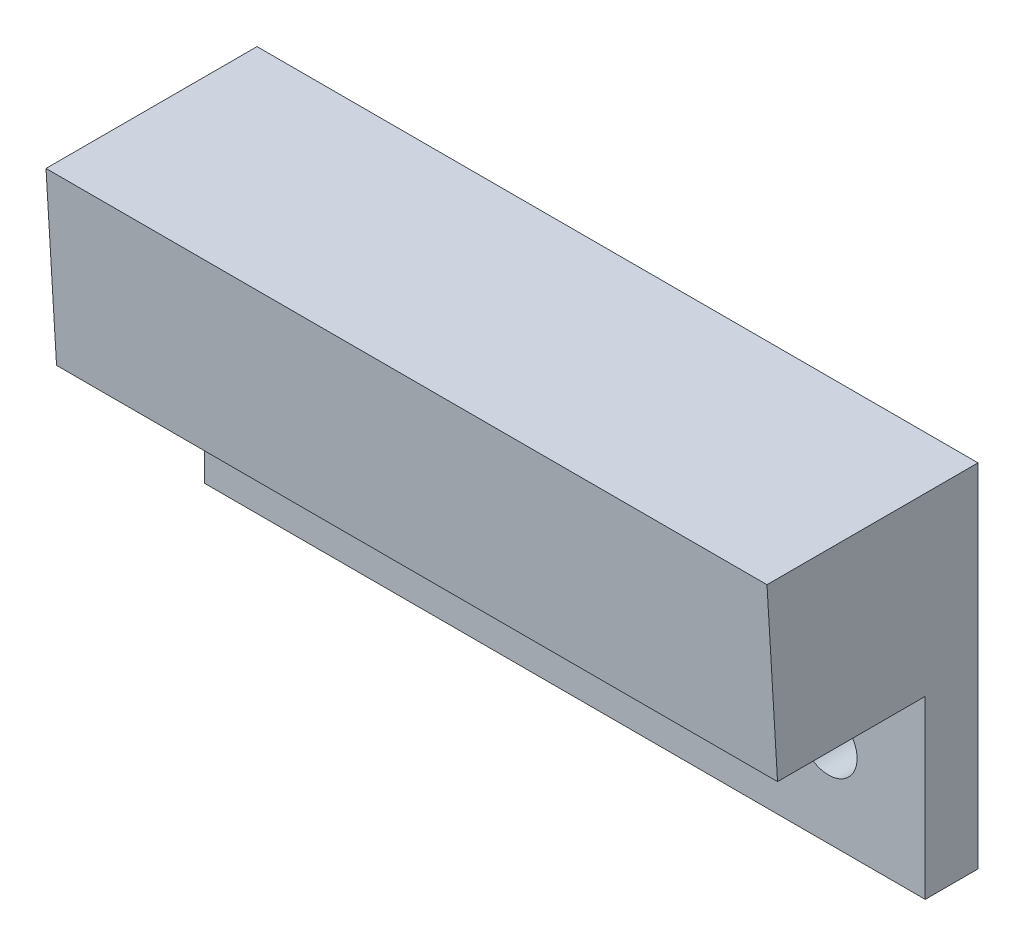
SolidWorks part; units mm, degrees
ref_plane "Plan de face" through (0, 0, 0) normal (0, 0, 1) x (1, 0, 0)
ref_plane "Plan de dessus" through (0, 0, 0) normal (0, 1, 0) x (1, 0, 0)
ref_plane "Plan de droite" through (0, 0, 0) normal (1, 0, 0) x (0, 0, -1)
sketch "Esquisse1" plane through (0, 0, 0) normal (0, 0, 1) x (1, 0, 0)
  line L1 (0, 0) -> (41, 0)
  line L2 (0, 0) -> (0, -10)
  line L3 (0, -10) -> (41, -10)
  line L4 (41, 0) -> (41, -10)
  dimension "D1" = 41
  dimension "D2" = 10
extrude "Boss.-Extru.1" add sketch "Esquisse1" along normal blind 12
sketch "Esquisse2" plane through (0, -10, 0) normal (0, -1, 0) x (1, 0, 0)
  line L0 (41, 12) -> (41, 0) construction
  line L1 (0, 0) -> (41, 0)
  line L2 (0, 0) -> (0, 3)
  line L3 (0, 3) -> (41, 3)
  line L4 (41, 0) -> (41, 3)
  dimension "D1" = 3
extrude "Boss.-Extru.2" add sketch "Esquisse2" along normal blind 10
sketch "Esquisse3" plane through (0, 0, 3) normal (0, 0, 1) x (1, 0, 0)
  line L0 (41, -20) -> (41, -10) construction
  line L1 (0, -20) -> (0, -10) construction
  circle A0 centre (5.5, -15) radius 1.625
  circle A1 centre (35.5, -15) radius 1.625
  point P6 (41, -15)
  dimension "D3" = 3.25
  dimension "D4" = 3.25
  dimension "D1" = 30
  dimension "D2" = 5.5
extrude "Enlèv. mat.-Extru.1" cut sketch "Esquisse3" against normal blind 10
sketch "Esquisse4" plane through (41, 0, 0) normal (1, 0, 0) x (0, 0, -1)
  line L0 (-12, 0) -> (-11.4, -10)
  line L1 (-12, -10) -> (-3, -10) construction
  line L2 (-11.4, -10) -> (-12, -10)
  line L3 (-12, -10) -> (-12, 0)
  dimension "D1" = 0.6
extrude "Enlèv. mat.-Extru.2" cut sketch "Esquisse4" against normal through all
